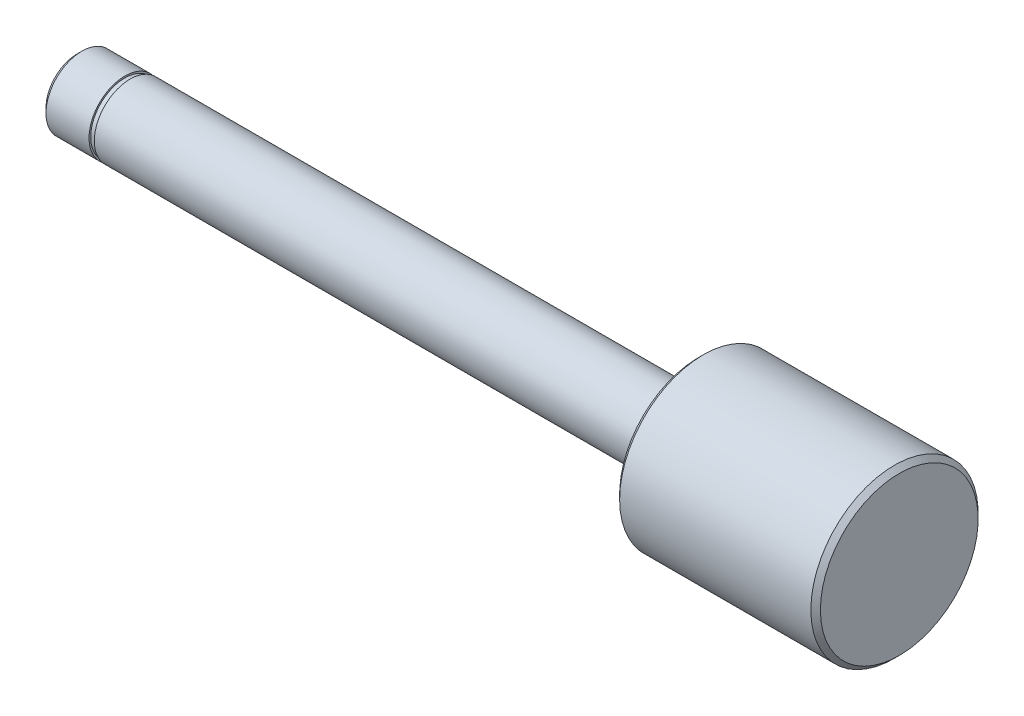
SolidWorks part; units mm, degrees
material "1.1191 (C45E)"
ref_plane "Plan de face" through (0, 0, 0) normal (0, 0, 1) x (1, 0, 0)
ref_plane "Plan de dessus" through (0, 0, 0) normal (0, 1, 0) x (1, 0, 0)
ref_plane "Plan de droite" through (0, 0, 0) normal (1, 0, 0) x (0, 0, -1)
sketch "Esquisse1" plane through (0, 0, 0) normal (0, 0, 1) x (1, 0, 0)
  line L0 (-86, 0) -> (86, 0) construction
  line L1 (-86, 0) -> (-86, 7.5)
  line L2 (-86, 7.5) -> (44, 7.5)
  line L3 (44, 7.5) -> (44, 17.5)
  line L4 (44, 17.5) -> (86, 17.5)
  line L5 (86, 17.5) -> (86, 0)
  line L6 (-86, 0) -> (86, 0)
  dimension "D1" = 15
  dimension "D2" = 35
  dimension "D3" = 130
  dimension "D4" = 42
  dimension "D5" = 172
revolve "Révolution1" add sketch "Esquisse1" angle 360 about L0
chamfer "Chanfrein1" distance 1 angle 45 3 edges at (86, 0, 17.5) (44, 0, 17.5) (-86, 0, 7.5)
sketch "Esquisse2" plane through (0, 0, 0) normal (0, 0, 1) x (1, 0, 0)
  line L0 (0, 0) -> (-52.5094, 0) construction
  line L1 (-76, 15.6541) -> (-74.9, 15.6541)
  line L2 (-76, 15.6541) -> (-76, 7.15)
  line L3 (-76, 7.15) -> (-74.9, 7.15)
  line L4 (-74.9, 15.6541) -> (-74.9, 7.15)
  line L5 (44, 16.5) -> (44, -16.5) construction
  dimension "D1" = 120
  dimension "D2" = 14.3
  dimension "D3" = 1.1
  dimension "D4" = 8.5041
revolve "Enlèvement de matière-Révolution1" cut sketch "Esquisse2" angle 360 about L0
